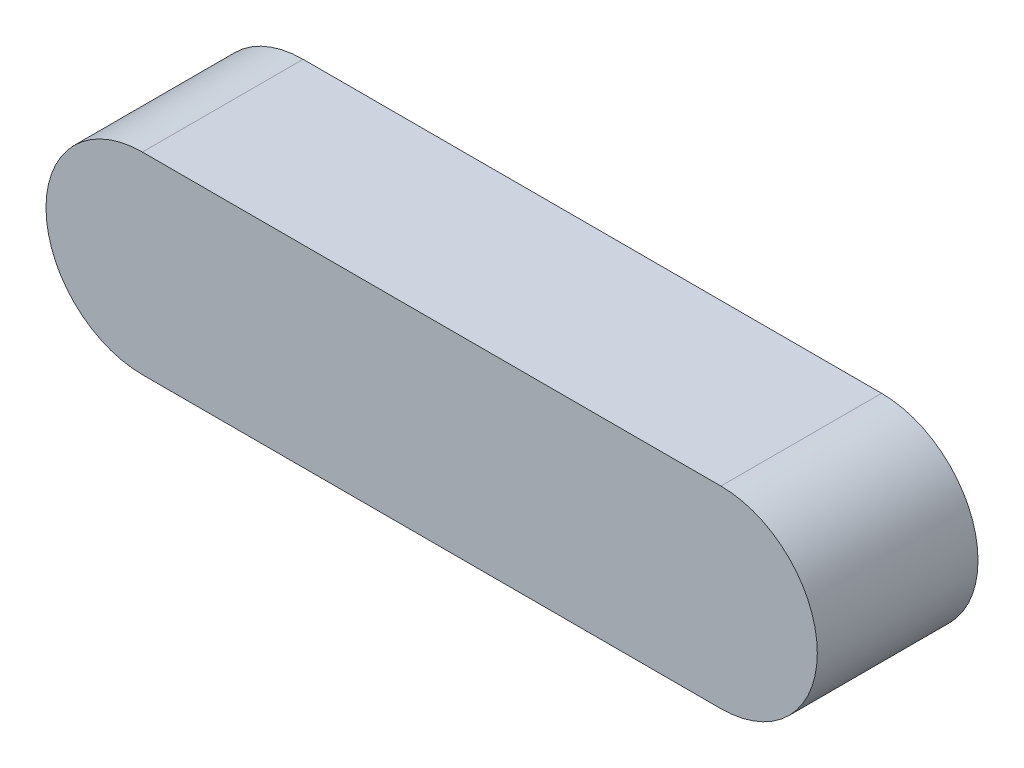
SolidWorks part; units mm, degrees
ref_plane "Front Plane" through (0, 0, 0) normal (0, 0, 1) x (1, 0, 0)
ref_plane "Top Plane" through (0, 0, 0) normal (0, 1, 0) x (1, 0, 0)
ref_plane "Right Plane" through (0, 0, 0) normal (1, 0, 0) x (0, 0, -1)
sketch "Sketch1" plane through (0, 0, 0) normal (0, 0, 1) x (1, 0, 0)
  line L0 (0, 0) -> (228.6, 0) construction
  line L1 (0, 38.1) -> (228.6, 38.1)
  line L2 (0, -38.1) -> (228.6, -38.1)
  arc A0 (0, 38.1) -> (0, -38.1) centre (0, 0) ccw
  arc A1 (228.6, -38.1) -> (228.6, 38.1) centre (228.6, 0) ccw
  point P3 (114.3, 0)
  point P8 (0, 0)
  point P9 (0, 0)
  point P10 (0, 0)
  point P11 (0, 0)
  point P12 (0, 0)
  point P13 (0, 0)
  dimension "D2" = 38.1
  dimension "D1" = 114.3
extrude "Boss-Extrude1" add sketch "Sketch1" along normal blind 63.5 contours L2 A1 L1 A0
